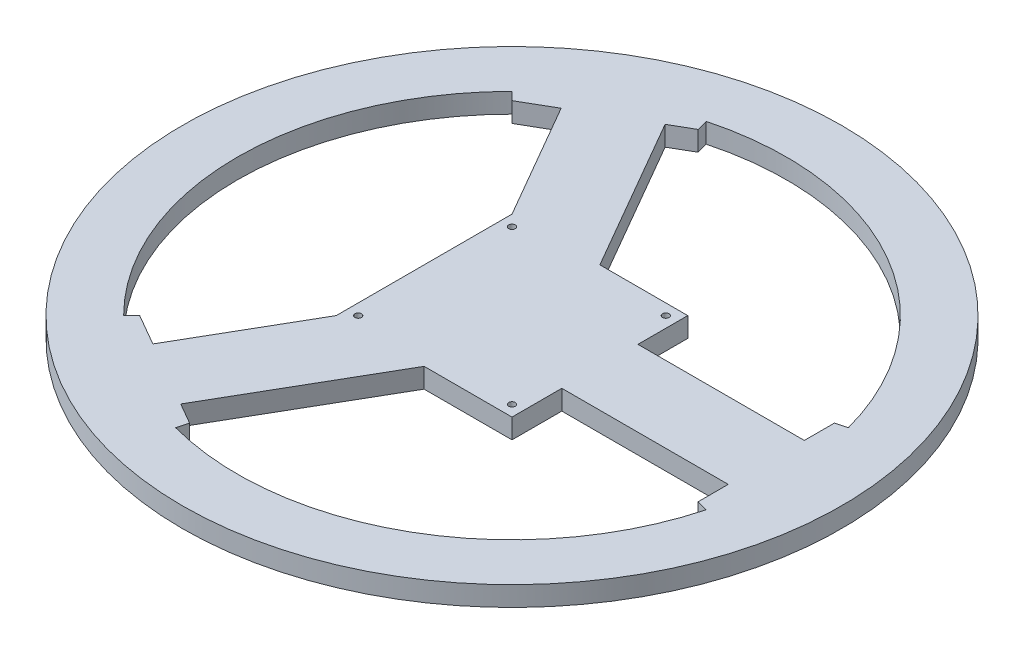
SolidWorks part; units mm, degrees
ref_plane "Alzado" through (0, 0, 0) normal (0, 0, 1) x (1, 0, 0)
ref_plane "Planta" through (0, 0, 0) normal (0, 1, 0) x (1, 0, 0)
ref_plane "Vista lateral" through (0, 0, 0) normal (1, 0, 0) x (0, 0, -1)
sketch "Croquis1" plane through (0, 0, 0) normal (0, 1, 0) x (1, 0, 0)
  line L0 (0, 0) -> (125, 0) construction
  line L1 (-150, 150) -> (150, 150) construction
  line L2 (-150, 150) -> (-150, -150) construction
  line L3 (-150, -150) -> (150, -150) construction
  line L4 (150, 150) -> (150, -150) construction
  line L5 (-150, 150) -> (150, -150) construction
  line L6 (-150, -150) -> (150, 150) construction
  circle A0 centre (0, 0) radius 150
  circle A1 centre (0, 0) radius 125
  point P0 (0, 0)
  dimension "D3" = 250
  dimension "D1" = 300
  dimension "D2" = 300
extrude "Saliente-Extruir1" add sketch "Croquis1" along normal blind 9
sketch "Croquis2" plane through (0, 0, 0) normal (0, 1, 0) x (1, 0, 0)
  line L0 (0, 0) -> (133.6051, 0) construction
  line L1 (120.7407, 32.3524) -> (146.4695, 32.3524)
  line L2 (120.7407, 32.3524) -> (120.7407, -32.3524) construction
  line L3 (120.7407, -32.3524) -> (146.4695, -32.3524)
  line L4 (146.4695, 32.3524) -> (146.4695, -32.3524)
  line L5 (120.7407, 32.3524) -> (146.4695, -32.3524) construction
  line L6 (120.7407, -32.3524) -> (146.4695, 32.3524) construction
  line L27 (120.7407, 32.3524) -> (0, 0) construction
  line L28 (0, 0) -> (120.7407, -32.3524) construction
  line L42 (120.7407, 32.3524) -> (115.7407, 31.0126)
  line L43 (115.7407, 31.0126) -> (115.7407, -31.0126)
  line L44 (115.7407, -31.0126) -> (120.7407, -32.3524)
  line L45 (-88.3883, -88.3883) -> (-101.2527, -110.6701)
  line L46 (-45.2168, -143.0225) -> (-101.2527, -110.6701)
  line L47 (-32.3524, -120.7407) -> (-45.2168, -143.0225)
  line L48 (-32.3524, -120.7407) -> (-31.0126, -115.7407)
  line L49 (-31.0126, -115.7407) -> (-84.7281, -84.7281)
  line L50 (-84.7281, -84.7281) -> (-88.3883, -88.3883)
  line L51 (-32.3524, 120.7407) -> (-45.2168, 143.0225)
  line L52 (-101.2527, 110.6701) -> (-45.2168, 143.0225)
  line L53 (-88.3883, 88.3883) -> (-101.2527, 110.6701)
  line L54 (-88.3883, 88.3883) -> (-84.7281, 84.7281)
  line L55 (-84.7281, 84.7281) -> (-31.0126, 115.7407)
  line L56 (-31.0126, 115.7407) -> (-32.3524, 120.7407)
  circle A1 centre (0, 0) radius 150 construction
  circle A2 centre (0, 0) radius 125 construction
  point P24 (0, 0)
  point P27 (0, 0)
  dimension "D2" = 5
  dimension "D3" = 3
  dimension "D4" = 30
extrude "Saliente-Extruir3" add sketch "Croquis2" along normal blind 9
sketch "Croquis3" plane through (0, 0, 0) normal (0, 1, 0) x (1, 0, 0)
  line L0 (-70.5499, 92.9139) -> (-40, 40)
  line L1 (-40, 40) -> (40, 40) construction
  line L2 (-40, 40) -> (-40, -40) construction
  line L3 (-40, -40) -> (40, -40) construction
  line L4 (40, 40) -> (40, -40) construction
  line L5 (-40, 40) -> (40, -40) construction
  line L6 (-40, -40) -> (40, 40) construction
  line L7 (-84.7281, 84.7281) -> (-31.0126, 115.7407) construction
  line L8 (-70.5499, 92.9139) -> (-40.5499, 110.2344)
  line L9 (-40.5499, 110.2344) -> (0, 40)
  line L10 (0, 40) -> (40, 40)
  line L11 (40, 40) -> (40, 17.32)
  line L12 (40, 17.32) -> (115.7407, 17.32)
  line L13 (115.7407, 31.0126) -> (115.7407, -31.0126) construction
  line L14 (115.7407, 17.32) -> (115.7407, -17.32)
  line L15 (115.7407, -17.32) -> (40, -17.32)
  line L16 (40, -17.32) -> (40, -40)
  line L17 (40, -40) -> (0, -40)
  line L18 (0, -40) -> (-40.5499, -110.2344)
  line L19 (-31.0126, -115.7407) -> (-84.7281, -84.7281) construction
  line L20 (-40.5499, -110.2344) -> (-70.5499, -92.9139)
  line L21 (-70.5499, -92.9139) -> (-40, -40)
  line L22 (-40, -40) -> (-40, 40)
  line L23 (0, 40) -> (0, -40) construction
  line L24 (40, 17.32) -> (40, -17.32) construction
  line L26 (-35, 35) -> (35, 35) construction
  line L27 (-35, 35) -> (-35, -35) construction
  line L28 (-35, -35) -> (35, -35) construction
  line L29 (35, 35) -> (35, -35) construction
  line L30 (-35, 35) -> (35, -35) construction
  line L31 (-35, -35) -> (35, 35) construction
  circle A0 centre (-35, 35) radius 1.5
  circle A1 centre (35, 35) radius 1.5
  circle A2 centre (35, -35) radius 1.5
  circle A3 centre (-35, -35) radius 1.5
  point P0 (0, 0)
  point P7 (0, 0)
  dimension "D6" = 3
  dimension "D1" = 80
  dimension "D2" = 60
  dimension "D3" = 60
  dimension "D4" = 34.64
  dimension "D5" = 17.32
  dimension "D7" = 70
extrude "Saliente-Extruir4" add sketch "Croquis3" along normal blind 9
sketch "Croquis4" plane through (0, 9, 0) normal (0, 1, 0) x (1, 0, 0)
  circle A0 centre (-35, 35) radius 1.5
  circle A1 centre (-35, 35) radius 2.5
  circle A2 centre (-35, 35) radius 1.5 construction
  dimension "D1" = 5
extrude "Saliente-Extruir5" [suppressed] add sketch "Croquis4" along normal blind 10
pattern_linear "MatrizL2" [suppressed] count 2 spacing 70 count 2 spacing 70
sketch "Croquis5" plane through (0, 9, 0) normal (0, 1, 0) x (1, 0, 0)
  circle A0 centre (0, 0) radius 109.4309
  circle A1 centre (0, 0) radius 170.2429
extrude "Cortar-Extruir1" [suppressed] cut sketch "Croquis5" against normal blind 10
